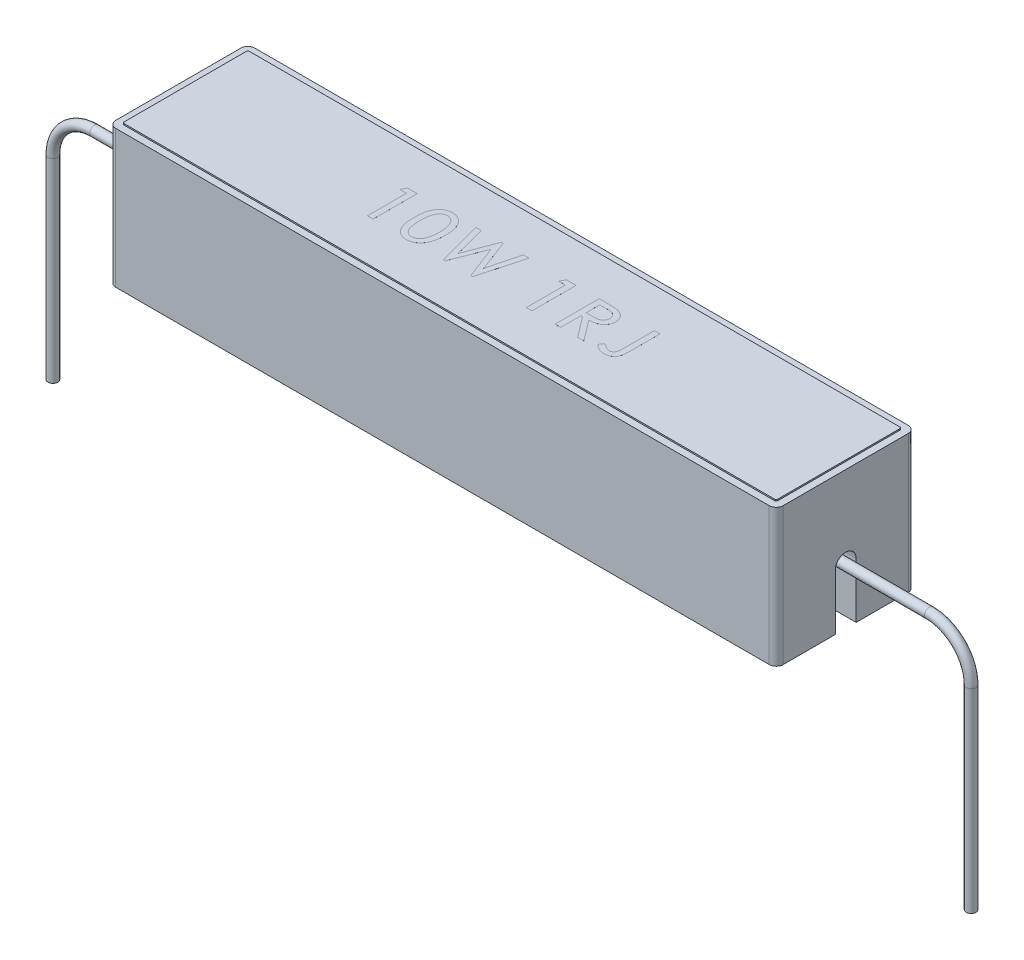
SolidWorks part; units mm, degrees
material "Ceramic Porcelain"
ref_plane "Front Plane" through (0, 0, 0) normal (0, 0, 1) x (1, 0, 0)
ref_plane "Top Plane" through (0, 0, 0) normal (0, 1, 0) x (1, 0, 0)
ref_plane "Right Plane" through (0, 0, 0) normal (1, 0, 0) x (0, 0, -1)
sketch "Sketch1" plane through (0, 0, 0) normal (0, 1, 0) x (1, 0, 0)
  line L1 (-24, 5) -> (24, 5)
  line L2 (-24, 5) -> (-24, -5)
  line L3 (-24, -5) -> (24, -5)
  line L4 (24, 5) -> (24, -5)
  line L5 (-24, 5) -> (24, -5) construction
  line L6 (-24, -5) -> (24, 5) construction
  point P0 (0, 0)
  dimension "D1" = 48
  dimension "D2" = 10
extrude "Boss-Extrude1" add sketch "Sketch1" along normal blind 10
sketch "Sketch2" plane through (24, 0, 0) normal (1, 0, 0) x (0, 0, -1)
  line L0 (0, 0) -> (0, 4) construction
  line L1 (-5, 0) -> (5, 0) construction
  line L2 (-0.75, 0) -> (-0.75, 4)
  line L3 (0.75, 0) -> (0.75, 4)
  arc A0 (-0.75, 0) -> (0.75, 0) centre (0, 0) ccw
  arc A1 (0.75, 4) -> (-0.75, 4) centre (0, 4) ccw
  point P4 (0, 2)
  dimension "D1" = 1.5
  dimension "D2" = 4
extrude "Cut-Extrude1" cut sketch "Sketch2" against normal blind 2
mirror "Mirror1" about plane through (0, 0, 0) normal (1, 0, 0) of "Cut-Extrude1"
sketch "Sketch3" plane through (0, 0, 0) normal (0, -1, 0) x (1, 0, 0)
  line L1 (-22, 3) -> (22, 3)
  line L2 (-22, 3) -> (-22, -3)
  line L3 (-22, -3) -> (22, -3)
  line L4 (22, 3) -> (22, -3)
  line L5 (-22, 3) -> (22, -3) construction
  line L6 (-22, -3) -> (22, 3) construction
  line L7 (-22, -0.75) -> (-22, 0.75) construction
  line L8 (-24, 5) -> (24, 5) construction
  point P0 (0, 0)
  dimension "D1" = 2
extrude "Cut-Extrude2" cut sketch "Sketch3" against normal blind 8
fillet "Fillet4" radius 0.5 4 edges at (-24, 5, -5) (-24, 5, 5) (24, 5, -5) (24, 5, 5)
sketch "Sketch7" plane through (0, 10, 0) normal (0, 1, 0) x (1, 0, 0)
  line L0 (23.5, 5) -> (-23.5, 5) construction
  line L1 (-23.5, 4.5) -> (23.5, 4.5)
  line L2 (-23.5, 4.5) -> (-23.5, -4.5)
  line L3 (-23.5, -4.5) -> (23.5, -4.5)
  line L4 (23.5, 4.5) -> (23.5, -4.5)
  line L5 (-23.5, 4.5) -> (23.5, -4.5) construction
  line L6 (-23.5, -4.5) -> (23.5, 4.5) construction
  line L7 (-24, 4.5) -> (-24, -4.5) construction
  point P0 (0, 0)
  dimension "D1" = 0.5
  dimension "D2" = 0.5
extrude "Cut-Extrude4" cut sketch "Sketch7" against normal blind 0.1 flip side to cut
fillet "Fillet5" radius 0.1 4 edges at (23.5, 9.95, 4.5) (23.5, 9.95, -4.5) (-23.5, 9.95, -4.5) (-23.5, 9.95, 4.5)
sketch "Sketch4" plane through (0, 8, 0) normal (0, -1, 0) x (1, 0, 0)
  line L4 (22, -3) -> (22, 3)
  line L5 (22, 3) -> (-22, 3)
  line L6 (-22, 3) -> (-22, -3)
  line L7 (-22, -3) -> (22, -3)
  line L8 (22, -3) -> (22, 3)
  line L9 (22, 3) -> (-22, 3)
  line L10 (-22, 3) -> (-22, -3)
  line L11 (-22, -3) -> (22, -3)
  dimension "D1" = 0
extrude "Boss-Extrude2" add sketch "Sketch4" along normal offset from surface (7.5 mm away) 0.5 separate body up to face at (0, 0, 2.8207)
fillet "Fillet2" radius 0.5 4 edges at (0, 0.5, -3) (-22, 0.5, 0) (0, 0.5, 3) (22, 0.5, 0)
fillet "Fillet3" radius 0.1 8 edges at (22, 4.5, -3) (22, 4.5, 3) (-22, 4.5, -3) (-22, 4.5, 3) (21.8536, 0.6464, -2.8536) (21.8536, 0.6464, 2.8536) (-21.8536, 0.6464, -2.8536) (-21.8536, 0.6464, 2.8536)
sketch "Sketch6" plane through (0, 0, 0) normal (1, 0, 0) x (0, 0, -1)
  line L0 (0, 0) -> (0, 4) construction
  circle A0 centre (0, 4) radius 0.35
  dimension "D1" = 0.7
extrude "Cut-Extrude3" cut sketch "Sketch6" against normal through all both and the other way through all
sketch "Sketch Adjust Wire Length" plane through (0, 0, 0) normal (0, 0, 1) x (1, 0, 0)
  line L0 (0, 0) -> (0, 4) construction
  line L1 (-23.5, 0) -> (23.5, 0) construction
  line L2 (-30.02, 4) -> (30.02, 4)
  line L3 (-33.02, 1) -> (-33.02, -13)
  line L4 (33.02, 1) -> (33.02, -13)
  line L5 (0, 0) -> (0, -13) construction
  line L6 (-33.02, -13) -> (33.02, -13) construction
  arc A0 (-30.02, 4) -> (-33.02, 1) centre (-30.02, 1) ccw
  arc A1 (30.02, 4) -> (33.02, 1) centre (30.02, 1) cw
  point P6 (43.5398, -13.3745)
  point P11 (-42.1778, -14.5232)
  dimension "D1" = 3
  dimension "D2" = 66.04
  dimension "D3" = 17
  dimension "D4" = 4
sketch "Sketch Wire Diameter" plane through (0, 0, 0) normal (1, 0, 0) x (0, 0, -1)
  circle A0 centre (0, 4) radius 0.35
  dimension "D1" = 0.7
sweep "Adjust Wire Size Length" add profiles "Sketch Wire Diameter" path "Sketch Adjust Wire Length"
sketch "Sketch10" plane through (0, 10, 0) normal (0, 1, 0) x (1, 0, 0)
  line L0 (0, -1.5) -> (0, 1.5) construction
  line L1 (-10, -1.5) -> (10, -1.5) construction
  text T0 "10W 1RJ" font "Century Gothic" height 3.175
  dimension "D1" = 3
  dimension "D2" = 20
extrude "Boss-Extrude3" add sketch "Sketch10" along normal blind 0.001
